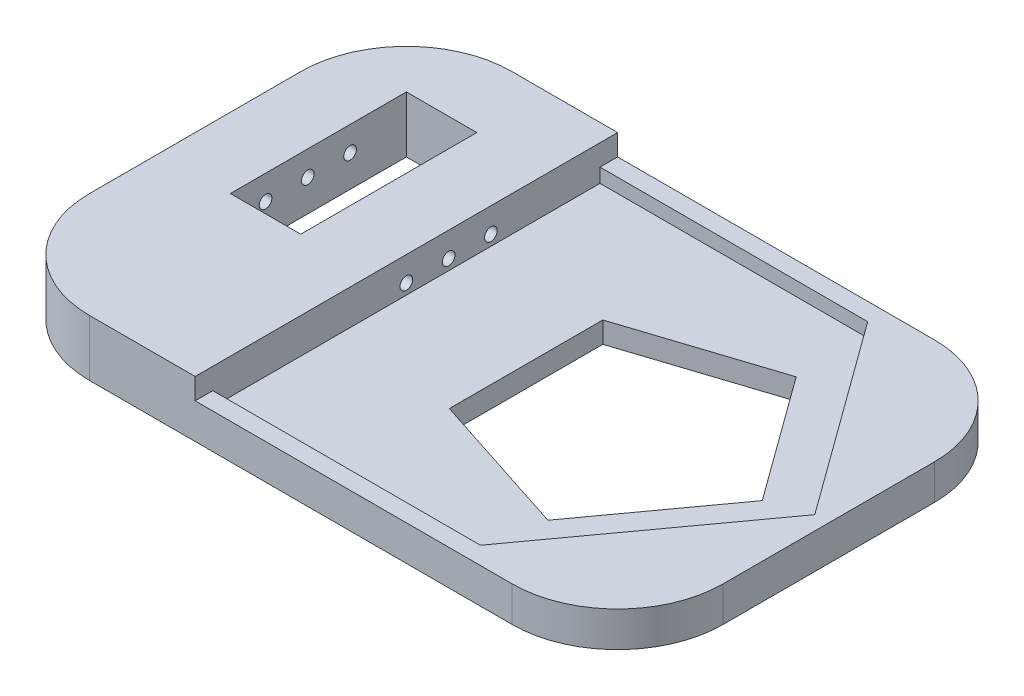
SolidWorks part; units mm, degrees
ref_plane "Front Plane" through (0, 0, 0) normal (0, 0, 1) x (1, 0, 0)
ref_plane "Top Plane" through (0, 0, 0) normal (0, 1, 0) x (1, 0, 0)
ref_plane "Right Plane" through (0, 0, 0) normal (1, 0, 0) x (0, 0, -1)
sketch "Sketch1" plane through (0, 0, 0) normal (0, 1, 0) x (1, 0, 0)
  line L1 (-45, 30) -> (45, 30)
  line L2 (-45, 30) -> (-45, -30)
  line L3 (-45, -30) -> (45, -30)
  line L4 (45, 30) -> (45, -30)
  line L5 (-45, 30) -> (45, -30) construction
  line L6 (-45, -30) -> (45, 30) construction
  point P0 (0, 0)
  dimension "D1" = 60
  dimension "D2" = 90
extrude "Boss-Extrude1" add sketch "Sketch1" against normal blind 3
sketch "Sketch2" plane through (0, 0, 0) normal (0, 1, 0) x (1, 0, 0)
  line L0 (45, 0) -> (-45, 0) construction
  line L1 (45, -30) -> (45, 30) construction
  line L2 (-45, 30) -> (-45, -30) construction
  line L3 (43, 0) -> (23.0201, 27.5)
  line L5 (45, 30) -> (-45, 30)
  line L6 (43, 0) -> (23.0201, -27.5)
  line L7 (45, 30) -> (45, -30)
  line L8 (-45, -27.5) -> (-45, -30)
  line L9 (23.0201, 27.5) -> (-15, 27.5)
  line L10 (23.0201, -27.5) -> (-15, -27.5)
  line L11 (-45, 27.5) -> (-45, 30)
  line L12 (45, -30) -> (-45, -30)
  line L13 (-15, 27.5) -> (-15, -27.5)
  line L14 (-45, -27.5) -> (-45, 27.5)
  line L15 (-2, 30) -> (-2, -30) construction
  dimension "D1" = 2
  dimension "D2" = 54
  dimension "D3" = 45
  dimension "D4" = 13
extrude "Boss-Extrude2" add sketch "Sketch2" along normal blind 2
sketch "Sketch4" plane through (0, 2, 0) normal (0, 1, 0) x (1, 0, 0)
  line L0 (-45, -30) -> (45, -30) construction
  line L1 (-45, 30) -> (-15, 30)
  line L2 (-45, 30) -> (-45, -30)
  line L3 (-45, -30) -> (-15, -30)
  line L4 (-15, 30) -> (-15, -30)
  line L5 (-15, 27.5) -> (-15, -27.5) construction
  dimension "D1" = 0
extrude "Boss-Extrude4" add sketch "Sketch4" along normal blind 3
sketch "Sketch5" plane through (-15, 0, 0) normal (1, 0, 0) x (0, 0, -1)
  line L0 (0, 5) -> (0, 0) construction
  line L1 (-30, 5) -> (30, 5) construction
  line L2 (27.5, 0) -> (-27.5, 0) construction
  line L3 (-30, 1.5) -> (30, 1.5) construction
  line L4 (-30, 5) -> (-30, 2) construction
  line L5 (30, 5) -> (30, 2) construction
  circle A0 centre (0, 1.5) radius 0.9
  circle A1 centre (6, 1.5) radius 0.9
  circle A2 centre (12, 1.5) radius 0.9
  dimension "D1" = 1.8
  dimension "D2" = 1.5
  dimension "D3" = 3
extrude "Cut-Extrude1" cut sketch "Sketch5" against normal blind 22
sketch "Sketch6" plane through (0, 5, 0) normal (0, 1, 0) x (1, 0, 0)
  line L0 (-15, 30) -> (-45, 30) construction
  line L1 (-35, 20) -> (-25, 20)
  line L2 (-35, 20) -> (-35, -5)
  line L3 (-35, -5) -> (-25, -5)
  line L4 (-25, 20) -> (-25, -5)
  line L5 (-45, 30) -> (-45, -30) construction
  dimension "D1" = 10
  dimension "D2" = 10
  dimension "D3" = 10
  dimension "D4" = 35
extrude "Cut-Extrude2" cut sketch "Sketch6" against normal through all
fillet "Fillet1" radius 15 4 edges at (-45, 1, -30) (-45, 1, 30) (45, -0.5, 30) (45, -0.5, -30)
sketch "Sketch7" plane through (0, 0, 0) normal (0, 1, 0) x (1, 0, 0)
  line L1 (35.541, 0) -> (22.7295, 17.6336)
  line L2 (22.7295, 17.6336) -> (2, 10.8981)
  line L3 (2, 10.8981) -> (2, -10.8981)
  line L4 (2, -10.8981) -> (22.7295, -17.6336)
  line L5 (22.7295, -17.6336) -> (35.541, 0)
  circle A0 centre (17, 0) radius 15 construction
  dimension "D1" = 26
extrude "Cut-Extrude3" cut sketch "Sketch7" against normal through all
